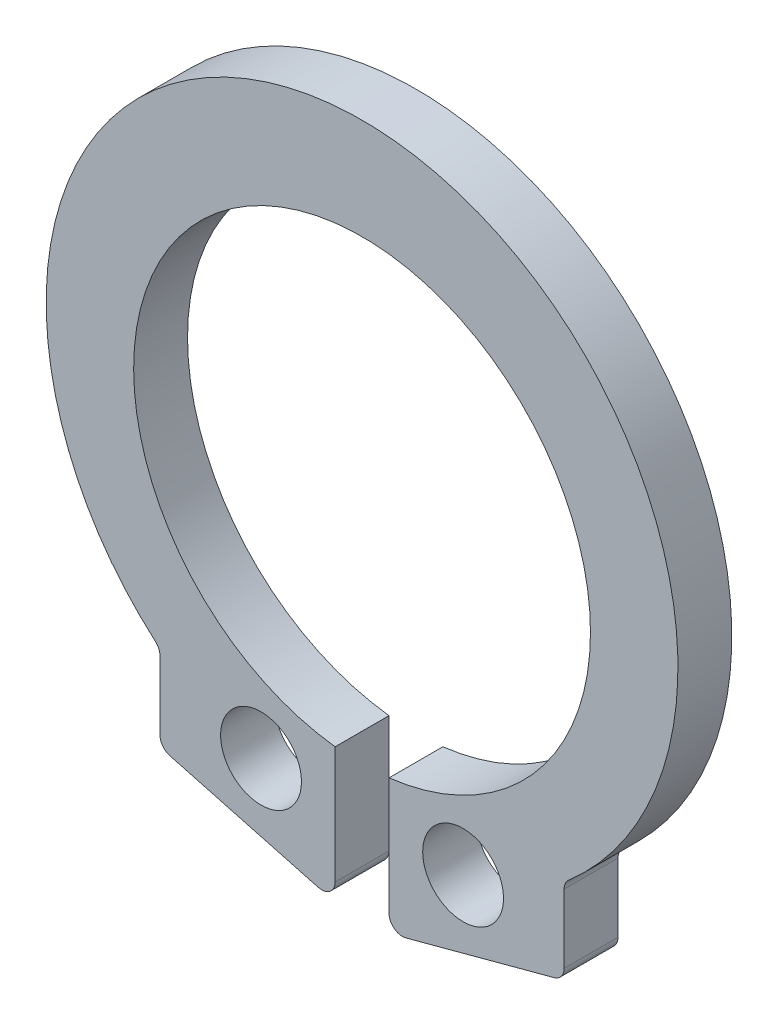
SolidWorks part; units mm, degrees
ref_plane "前视基准面" through (0, 0, 0) normal (0, 0, 1) x (1, 0, 0)
ref_plane "上视基准面" through (0, 0, 0) normal (0, 1, 0) x (1, 0, 0)
ref_plane "右视基准面" through (0, 0, 0) normal (1, 0, 0) x (0, 0, -1)
sketch "草图1" plane through (0, 0, 0) normal (0, 0, 1) x (1, 0, 0)
  line L0 (0, 10.1267) -> (0, -9.2778) construction
  line L1 (-7.7667, 0) -> (10.08, 0) construction
  line L3 (-0.4, -3.5676) -> (-0.4, -5.5676)
  line L4 (-0.4, -5.5676) -> (-3, -4.871)
  line L5 (-3, -4.871) -> (-3, -3.605)
  line L6 (0.4, -3.5676) -> (0.4, -5.5676)
  line L7 (0.4, -5.5676) -> (3, -4.871)
  line L8 (3, -4.871) -> (3, -3.605)
  arc A2 (0.4, -3.5676) -> (-0.4, -3.5676) centre (0, -0.2) ccw
  circle A3 centre (-1.5, -4.2676) radius 0.6
  circle A4 centre (1.5, -4.2676) radius 0.6
  arc A5 (3, -3.605) -> (-3, -3.605) centre (0, 0) ccw
  dimension "D1" = 0.8
  dimension "D2" = 0.2
  dimension "D4" = 15
  dimension "D5" = 1.2
  dimension "D8" = 0.7
  dimension "D9" = 1.5
  dimension "D6" = 3
  dimension "D7" = 2
extrude "凸台-拉伸1" add sketch "草图1" along normal blind 0.8
fillet "圆角1" radius 0.2 6 edges at (3, -3.605, 0.4) (3, -4.871, 0.4) (-3, -3.605, 0.4) (-3, -4.871, 0.4) (-0.4, -5.5676, 0.4) (0.4, -5.5676, 0.4)
